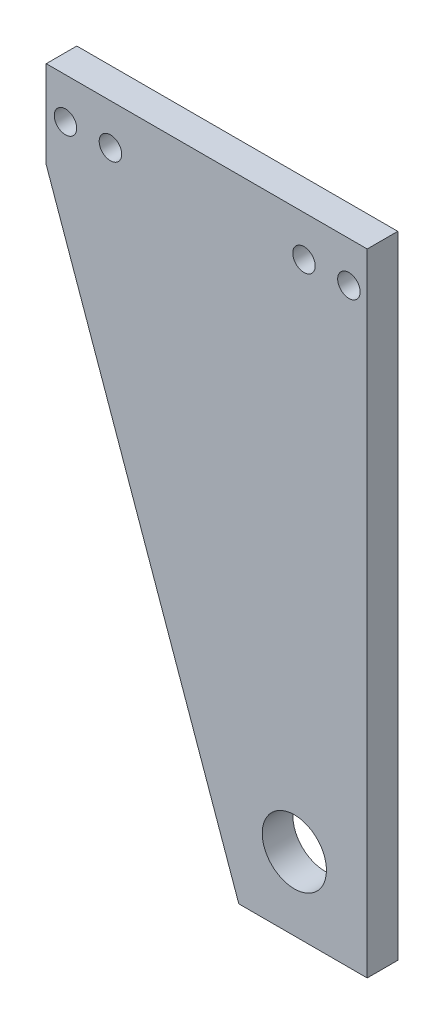
SolidWorks part; units mm, degrees
ref_plane "Alzado" through (0, 0, 0) normal (0, 0, 1) x (1, 0, 0)
ref_plane "Planta" through (0, 0, 0) normal (0, 1, 0) x (1, 0, 0)
ref_plane "Vista lateral" through (0, 0, 0) normal (1, 0, 0) x (0, 0, -1)
sketch "Croquis1" plane through (0, 0, 0) normal (0, 0, 1) x (1, 0, 0)
  line L0 (0, 0) -> (0, -98.35)
  line L1 (0, -98.35) -> (-20, -98.35)
  line L2 (-20, -98.35) -> (-50, -13.6326)
  line L3 (-50, 0) -> (0, 0)
  line L4 (0, -6.35) -> (-50, -6.35) construction
  line L5 (-50, 0) -> (-50, -13.6326)
  circle A0 centre (-2.85, -6.35) radius 1.75
  circle A1 centre (-9.85, -6.35) radius 1.75
  circle A2 centre (-40, -6.35) radius 1.75
  circle A3 centre (-47, -6.35) radius 1.75
  circle A4 centre (-11.35, -87) radius 5
  dimension "D3" = 3.5
  dimension "D4" = 3.5
  dimension "D5" = 3.5
  dimension "D6" = 3.5
  dimension "D7" = 6.35
  dimension "D8" = 2.85
  dimension "D9" = 7
  dimension "D10" = 19.5
  dimension "D11" = 10
  dimension "D12" = 11.35
  dimension "D13" = 11.35
  dimension "D14" = 7
  dimension "D17" = 3
  dimension "D2" = 98.35
  dimension "D15" = 20
  dimension "D16" = 50
extrude "Saliente-Extruir1" add sketch "Croquis1" along normal blind 4.7625
